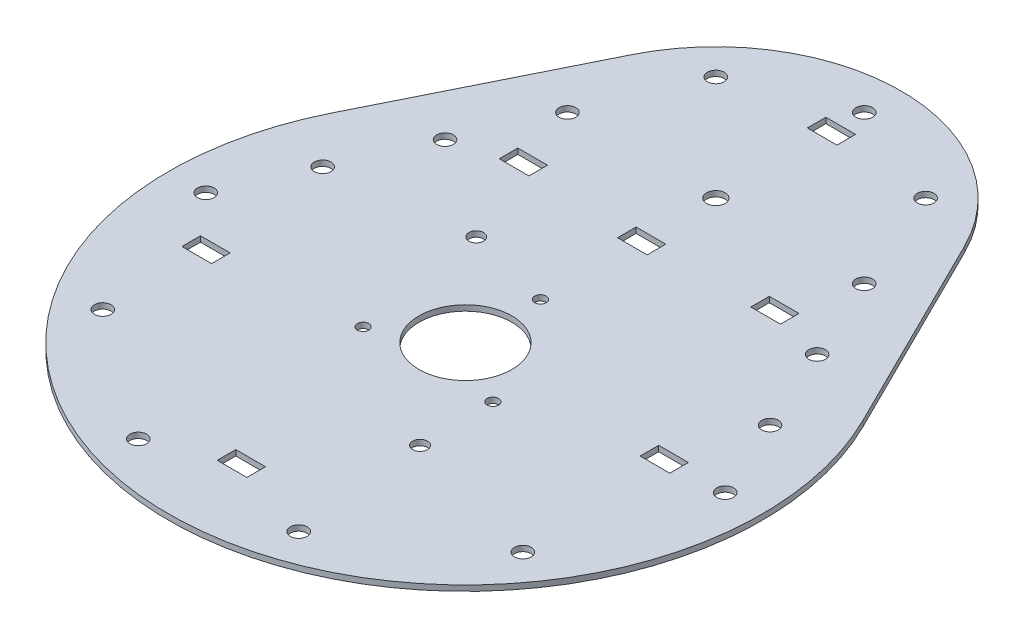
SolidWorks part; units mm, degrees
ref_plane "Front Plane" through (0, 0, 0) normal (0, 0, 1) x (1, 0, 0)
ref_plane "Top Plane" through (0, 0, 0) normal (0, 1, 0) x (1, 0, 0)
ref_plane "Right Plane" through (0, 0, 0) normal (1, 0, 0) x (0, 0, -1)
sketch "Sketch1" plane through (0, 0, 0) normal (0, 1, 0) x (1, 0, 0)
  line L0 (0, 67.5) -> (0, 0) construction
  line L1 (17.5, -10.1036) -> (0, 20.2073) construction
  line L2 (0, 20.2073) -> (-17.5, -10.1036) construction
  line L3 (-17.5, -10.1036) -> (17.5, -10.1036) construction
  line L4 (44.7903, 89.7222) -> (71.6645, 35.5556)
  line L5 (-44.7903, 89.7222) -> (-71.6645, 35.5556)
  line L6 (40, 67.5) -> (70, 0) construction
  line L7 (-4, 45) -> (4, 45)
  line L8 (-4, 45) -> (-4, 50)
  line L9 (-4, 50) -> (4, 50)
  line L10 (4, 45) -> (4, 50)
  line L11 (-4, 45) -> (4, 50) construction
  line L12 (-4, 50) -> (4, 45) construction
  line L13 (-40, 67.5) -> (-70, 0) construction
  line L14 (-5.9945, -60.9204) -> (2.0055, -60.9204)
  line L15 (-38.3758, 52.5) -> (-30.3758, 52.5)
  line L16 (-38.3758, 52.5) -> (-38.3758, 47.5)
  line L17 (-38.3758, 47.5) -> (-30.3758, 47.5)
  line L18 (-30.3758, 52.5) -> (-30.3758, 47.5)
  line L19 (-38.3758, 52.5) -> (-30.3758, 47.5) construction
  line L20 (-38.3758, 47.5) -> (-30.3758, 52.5) construction
  line L21 (30.1365, 46.7901) -> (38.1365, 46.7901)
  line L22 (30.1365, 46.7901) -> (30.1365, 51.7901)
  line L23 (30.1365, 51.7901) -> (38.1365, 51.7901)
  line L24 (38.1365, 46.7901) -> (38.1365, 51.7901)
  line L25 (30.1365, 46.7901) -> (38.1365, 51.7901) construction
  line L26 (30.1365, 51.7901) -> (38.1365, 46.7901) construction
  line L27 (-5.9945, -60.9204) -> (-5.9945, -55.9204)
  line L28 (-5.9945, -55.9204) -> (2.0055, -55.9204)
  line L29 (2.0055, -60.9204) -> (2.0055, -55.9204)
  line L30 (50.013, -2.9205) -> (58.013, -2.9205)
  line L31 (50.013, -2.9205) -> (50.013, 2.0795)
  line L32 (50.013, 2.0795) -> (58.013, 2.0795)
  line L33 (58.013, -2.9205) -> (58.013, 2.0795)
  line L34 (-60.6738, -15.7602) -> (-52.6738, -15.7602)
  line L35 (-60.6738, -15.7602) -> (-60.6738, -10.7602)
  line L36 (-60.6738, -10.7602) -> (-52.6738, -10.7602)
  line L37 (-52.6738, -15.7602) -> (-52.6738, -10.7602)
  line L38 (-4.0466, 96.2118) -> (3.9534, 96.2118)
  line L39 (-4.0466, 96.2118) -> (-4.0466, 101.2118)
  line L40 (-4.0466, 101.2118) -> (3.9534, 101.2118)
  line L41 (3.9534, 96.2118) -> (3.9534, 101.2118)
  circle A0 centre (0, 0) radius 12.525
  circle A1 centre (0, 0) radius 10.1036 construction
  circle A2 centre (-17.5, -10.1036) radius 1.55
  circle A3 centre (17.5, -10.1036) radius 1.55
  circle A4 centre (0, 20.2073) radius 1.55
  arc A6 (-71.6645, 35.5556) -> (71.6645, 35.5556) centre (0, 0) ccw
  circle A7 centre (0, 67.5) radius 2.5
  arc A8 (44.7903, 89.7222) -> (-44.7903, 89.7222) centre (0, 67.5) ccw
  circle A9 centre (0, 0) radius 35 construction
  circle A10 centre (0, 67.5) radius 15 construction
  circle A11 centre (0, 0) radius 45 construction
  circle A12 centre (0, 67.5) radius 22.5 construction
  circle A14 centre (40, 67.5) radius 2.25
  circle A15 centre (70, 0) radius 2.25
  circle A16 centre (56.6312, -41.145) radius 2.25
  circle A17 centre (21.6312, -66.574) radius 2.25
  circle A18 centre (-21.6312, -66.574) radius 2.25
  circle A19 centre (-56.6312, -41.145) radius 2.25
  circle A20 centre (-70, 0) radius 2.25
  circle A21 centre (28.2843, 95.7843) radius 2.25
  circle A22 centre (0, 107.5) radius 2.25
  circle A23 centre (-28.2843, 95.7843) radius 2.25
  circle A24 centre (-40, 67.5) radius 2.25
  circle A25 centre (-50.1535, 44.6547) radius 2.25
  circle A26 centre (-60.3069, 21.8094) radius 2.25
  circle A27 centre (50.1535, 44.6547) radius 2.25
  circle A28 centre (60.3069, 21.8094) radius 2.25
  circle A30 centre (17.8596, -30.1004) radius 2
  circle A31 centre (-23.2495, 26.1622) radius 2
  point P11 (0, 21.0074)
  point P21 (0, 47.5)
  point P42 (0, 0)
  point P51 (0, 67.5)
  point P62 (34.1365, 49.2901)
  point P63 (-34.3758, 50)
  dimension "D1" = 25.05
  dimension "D3" = 3.1
  dimension "D4" = 4.5
  dimension "D5" = 50
  dimension "D6" = 5
  dimension "D7" = 70
  dimension "D8" = 30
  dimension "D12" = 90
  dimension "D13" = 45
  dimension "D14" = 40
  dimension "D15" = 80
  dimension "D16" = 4.5
  dimension "D22" = 4
  dimension "D23" = 4
  dimension "D24" = 20
  dimension "D2" = 35
  dimension "D9" = 5
  dimension "D10" = 8
  dimension "D11" = 20
  dimension "D17" = 70
  dimension "D25" = 24
  dimension "D26" = 8
  dimension "D27" = 5
  dimension "D28" = 8
  dimension "D29" = 5
  dimension "D20" = 3
  dimension "D21" = 3
  dimension "D18" = 6
  dimension "D19" = 5
extrude "Boss-Extrude1" add sketch "Sketch1" along normal blind 1.5
